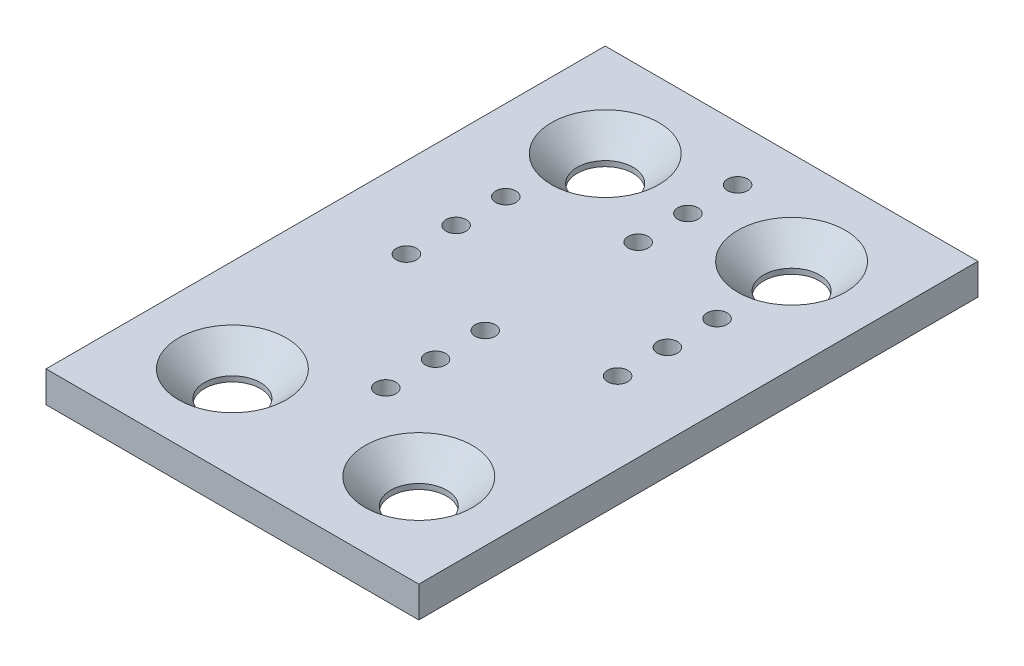
SolidWorks part; units mm, degrees
ref_plane "Front Plane" through (0, 0, 0) normal (0, 0, 1) x (1, 0, 0)
ref_plane "Top Plane" through (0, 0, 0) normal (0, 1, 0) x (1, 0, 0)
ref_plane "Right Plane" through (0, 0, 0) normal (1, 0, 0) x (0, 0, -1)
sketch "Sketch2" plane through (0, 0, 0) normal (0, 1, 0) x (1, 0, 0)
  line L0 (-17, 0) -> (17, 0)
  line L1 (0, 20.3091) -> (0, -20.3091)
  line L3 (-30, -45) -> (30, -45)
  line L4 (-30, -45) -> (-30, 45)
  line L5 (-30, 45) -> (30, 45)
  line L6 (30, -45) -> (30, 45)
  line L7 (-30, -45) -> (30, 45) construction
  line L8 (-30, 45) -> (30, -45) construction
  circle A0 centre (0, 20.3091) radius 1.625
  circle A1 centre (0, -20.3091) radius 1.625
  circle A2 centre (17, 0) radius 1.625
  circle A3 centre (-17, 0) radius 1.625
  circle A4 centre (0, 28.3091) radius 1.625
  circle A5 centre (17, 8) radius 1.625
  circle A6 centre (-17, 8) radius 1.625
  circle A7 centre (0, -12.3091) radius 1.625
  circle A8 centre (0, 36.3091) radius 1.625
  circle A9 centre (17, 16) radius 1.625
  circle A10 centre (-17, 16) radius 1.625
  circle A11 centre (0, -4.3091) radius 1.625
  point P0 (0, 0)
  point P4 (0, 0)
  point P8 (0, 0)
  dimension "D1" = 3.25
  dimension "D2" = 60
  dimension "D3" = 90
  dimension "D4" = 34
  dimension "D5" = 3
extrude "Boss-Extrude1" add sketch "Sketch2" along normal blind 5
sketch "Sketch3" plane through (0, 5, 0) normal (0, 1, 0) x (1, 0, 0)
  line L1 (-15, -30) -> (15, -30)
  line L2 (-15, -30) -> (-15, 30)
  line L3 (-15, 30) -> (15, 30)
  line L4 (15, -30) -> (15, 30)
  line L5 (-15, -30) -> (15, 30) construction
  line L6 (-15, 30) -> (15, -30) construction
  circle A0 centre (-15, 30) radius 3.375
  circle A1 centre (15, 30) radius 3.375
  circle A2 centre (15, -30) radius 3.375
  circle A3 centre (-15, -30) radius 3.375
  point P0 (0, 0)
  dimension "D1" = 30
  dimension "D2" = 60
extrude "Cut-Extrude1" cut sketch "Sketch3" against normal blind 5 contours A0 | A1 | A2 | A3
hole_wizard "CSK for M8 Countersunk Flat Head Screw1" positions "3DSketch1" profile "Sketch4" countersink size "M8" standard "ISO" end condition through all
sketch3d "3DSketch1"
  line L0 (-15, 0, 30) -> (-15, 5, 30) construction
  line L1 (15, 0, 30) -> (15, 5, 30) construction
  line L2 (-15, 0, -30) -> (-15, 5, -30) construction
  line L3 (15, 0, -30) -> (15, 5, -30) construction
  point P0 (-15, 5, 30)
  point P4 (15, 5, 30)
  point P8 (-15, 5, -30)
  point P12 (15, 5, -30)
sketch "Sketch4" plane through (-15, 5, 30) normal (1, 0, 0) x (0, 0, 1)
  line L0 (0, 0) -> (0, 5)
  line L1 (0, 5) -> (4.5, 5)
  line L2 (4.5, 5) -> (4.5, 4.15)
  line L3 (4.5, 4.15) -> (8.65, 0)
  line L5 (8.65, 0) -> (0, 0)
  line L6 (-4.5, 4.15) -> (-8.65, 0) construction
  line L11 (0, -6.35) -> (0, 107.95) construction
  dimension "Thru Hole Dia." = 9
  dimension "Thru Hole Depth" = 5
  dimension "Near C'Sink Dia." = 17.3
  dimension "Near C'Sink Angle" = 90
